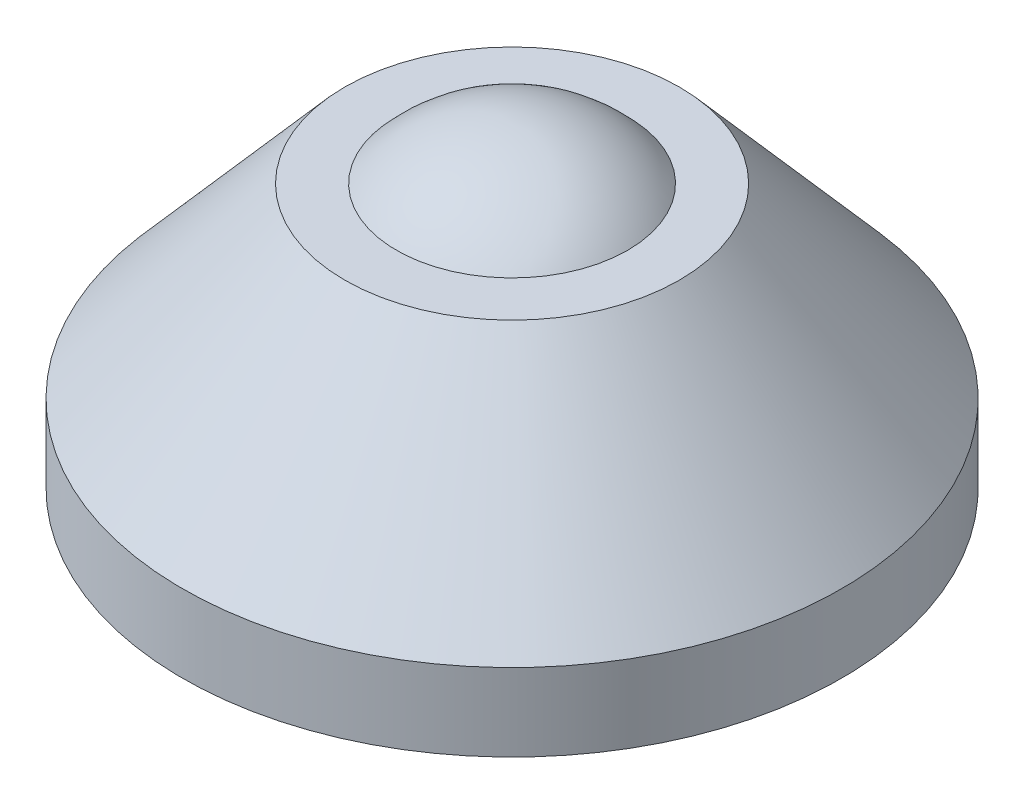
SolidWorks part; units mm, degrees
ref_plane "Plan de face" through (0, 0, 0) normal (0, 0, 1) x (1, 0, 0)
ref_plane "Plan de dessus" through (0, 0, 0) normal (0, 1, 0) x (1, 0, 0)
ref_plane "Plan de droite" through (0, 0, 0) normal (1, 0, 0) x (0, 0, -1)
sketch "Esquisse1" plane through (0, 0, 0) normal (0, 0, 1) x (1, 0, 0)
  line L0 (12.75, -3.2) -> (12.75, -6.2)
  line L1 (4.4721, 4) -> (6.4721, 4)
  line L2 (6.4721, 4) -> (12.75, -3.2)
  line L3 (12.75, -6.2) -> (1.5, -6.2)
  line L4 (1.5, -6.2) -> (1.5, -10.7)
  line L5 (1.5, -10.7) -> (0, -10.7)
  line L6 (0, 6) -> (0, -10.7) construction
  line L7 (0, 6) -> (0, -10.7)
  arc A0 (0, 6) -> (4.4721, 4) centre (0, 0) cw
  dimension "D1" = 6
  dimension "D2" = 25.5
  dimension "D3" = 3
  dimension "D4" = 12.2
  dimension "D5" = 3
  dimension "D6" = 4.5
  dimension "D7" = 2
  dimension "D8" = 10.2
revolve "Révolution1" add sketch "Esquisse1" angle 360 about L6
